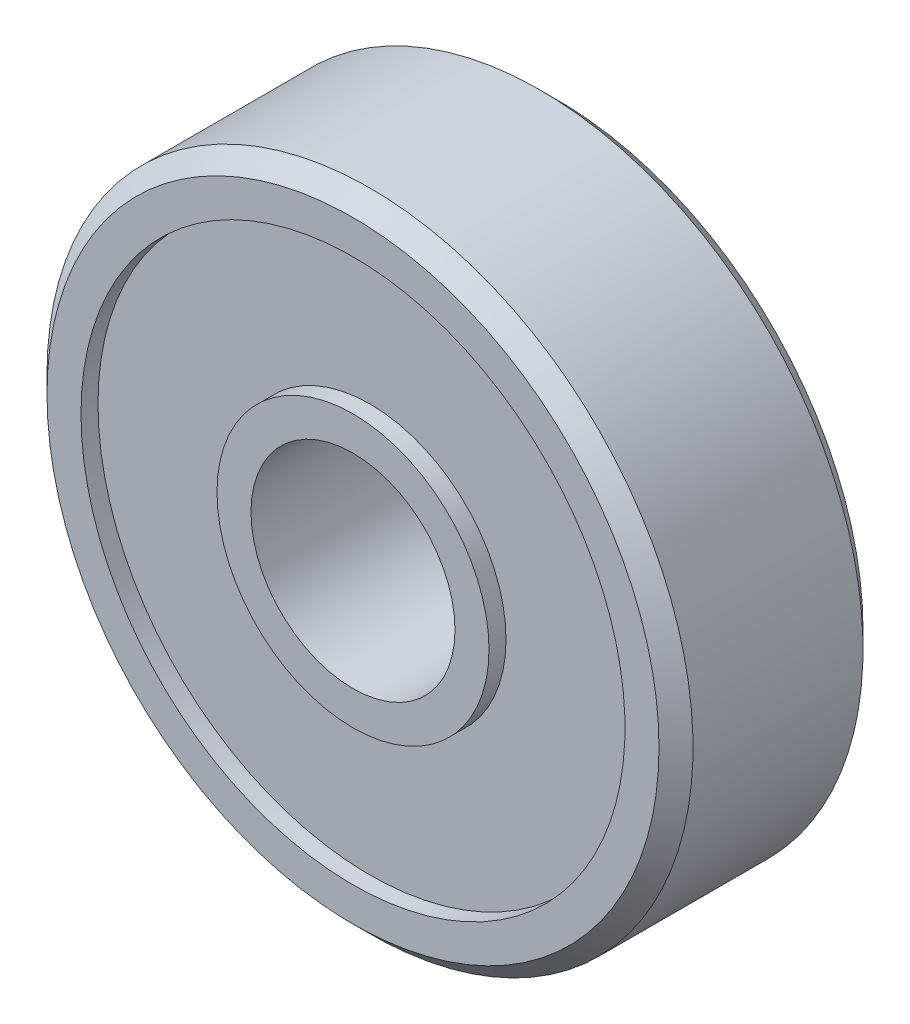
SolidWorks part; units mm, degrees
ref_plane "Front Plane" through (0, 0, 0) normal (0, 0, 1) x (1, 0, 0)
ref_plane "Top Plane" through (0, 0, 0) normal (0, 1, 0) x (1, 0, 0)
ref_plane "Right Plane" through (0, 0, 0) normal (1, 0, 0) x (0, 0, -1)
ref_plane "Plane1" through (0, 0, 0) normal (0, -1, 0) x (1, 0, 0)
sketch "Sketch1" plane through (0, 0, 0) normal (0, -1, 0) x (1, 0, 0)
  line L0 (9.5, 1) -> (9, 1.5)
  line L1 (9, 1.5) -> (8, 1.5)
  line L2 (8, 1.5) -> (8, 1)
  line L3 (8, 1) -> (4, 1)
  line L4 (4, 1) -> (4, 1.5)
  line L5 (4, 1.5) -> (3, 1.5)
  line L6 (3, 1.5) -> (3, -4.5)
  line L7 (3, -4.5) -> (4, -4.5)
  line L8 (4, -4.5) -> (4, -4)
  line L9 (4, -4) -> (8, -4)
  line L10 (8, -4) -> (8, -4.5)
  line L11 (8, -4.5) -> (9, -4.5)
  line L12 (9, -4.5) -> (9.5, -4)
  line L13 (9.5, -4) -> (9.5, 1)
  line L14 (0, 0.5) -> (0, -4.5) construction
  dimension "D1" = 6
  dimension "D2" = 0.5
  dimension "D3" = 8
  dimension "D4" = 6
  dimension "D5" = 0.5
  dimension "D6" = 45
  dimension "D7" = 0.5
  dimension "D8" = 45
  dimension "D9" = 16
  dimension "D10" = 19
revolve "Revolve1" add sketch "Sketch1" angle 360 about L14
